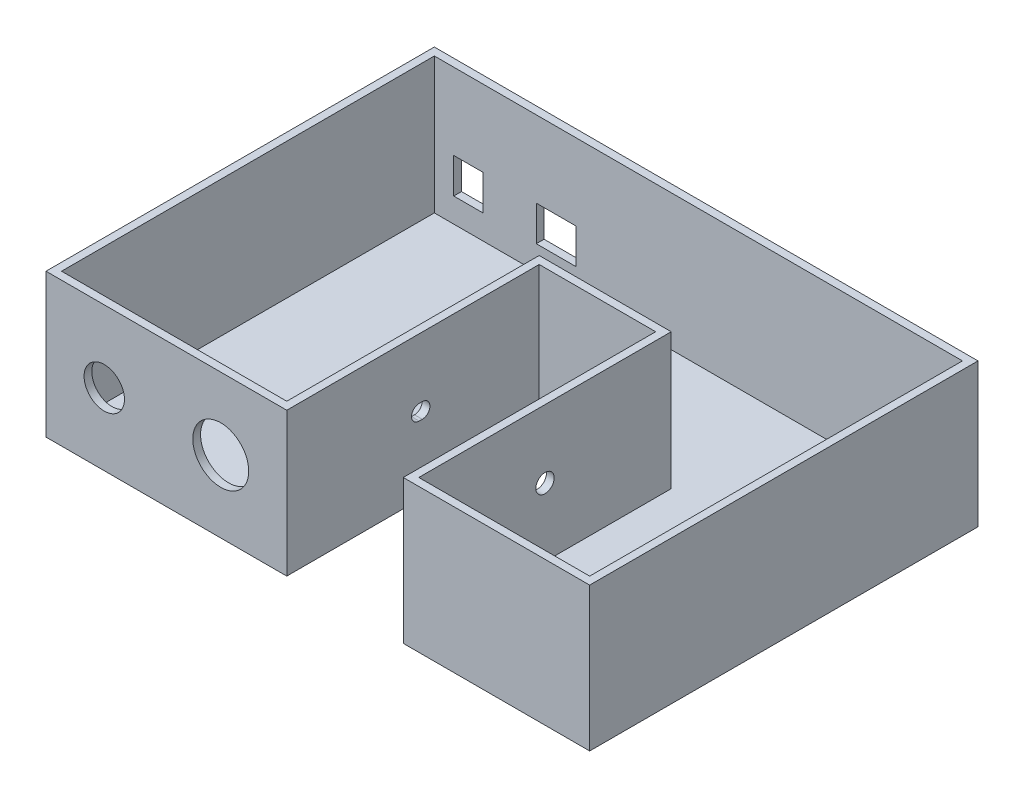
SolidWorks part; units mm, degrees
ref_plane "Front" through (0, 0, 0) normal (0, 0, 1) x (1, 0, 0)
ref_plane "Top" through (0, 0, 0) normal (0, 1, 0) x (1, 0, 0)
ref_plane "Right" through (0, 0, 0) normal (1, 0, 0) x (0, 0, -1)
sketch "Sketch1" plane through (0, 0, 0) normal (0, 1, 0) x (1, 0, 0)
  line L1 (0, 0) -> (78.74, 0)
  line L2 (0, 0) -> (0, 127)
  line L3 (0, 127) -> (78.74, 127)
  line L4 (78.74, 0) -> (78.74, 127)
  line L5 (78.74, 127) -> (116.84, 127)
  line L6 (78.74, 127) -> (78.74, 82.55)
  line L7 (78.74, 82.55) -> (116.84, 82.55)
  line L8 (116.84, 127) -> (116.84, 82.55)
  line L9 (116.84, 127) -> (177.8, 127)
  line L10 (116.84, 127) -> (116.84, 0)
  line L11 (116.84, 0) -> (177.8, 0)
  line L12 (177.8, 127) -> (177.8, 0)
  dimension "D1" = 127
  dimension "D2" = 78.74
  dimension "D3" = 38.1
  dimension "D4" = 44.45
  dimension "D5" = 127
  dimension "D6" = 60.96
extrude "Boss-Extrude1" add sketch "Sketch1" along normal blind 2.54 contours L1 L4 L3 L2 | L8 L5 L4 L7 | L12 L9 L8 L10 L11
sketch "Sketch2" plane through (0, 2.54, 0) normal (0, 1, 0) x (1, 0, 0)
  line L0 (119.38, 2.54) -> (175.26, 2.54)
  line L1 (0, 0) -> (78.74, 0) construction
  line L2 (2.54, 124.46) -> (175.26, 124.46)
  line L3 (2.54, 124.46) -> (2.54, 2.54)
  line L4 (2.54, 2.54) -> (76.2, 2.54)
  line L5 (76.2, 85.09) -> (76.2, 2.54)
  line L6 (116.84, 0) -> (177.8, 0) construction
  line L7 (175.26, 124.46) -> (175.26, 2.54)
  line L8 (78.74, 0) -> (78.74, 82.55) construction
  line L9 (119.38, 85.09) -> (119.38, 2.54)
  line L10 (0, 0) -> (0, 127) construction
  line L11 (0, 127) -> (177.8, 127) construction
  line L12 (177.8, 127) -> (177.8, 0) construction
  line L13 (116.84, 82.55) -> (116.84, 0) construction
  line L14 (0, 127) -> (0, 0)
  line L15 (0, 0) -> (78.74, 0)
  line L16 (78.74, 0) -> (78.74, 82.55)
  line L17 (78.74, 82.55) -> (116.84, 82.55)
  line L19 (76.2, 85.09) -> (119.38, 85.09)
  line L20 (78.74, 82.55) -> (116.84, 82.55) construction
  line L21 (116.84, 82.55) -> (116.84, 0)
  line L22 (116.84, 0) -> (177.8, 0)
  line L23 (177.8, 0) -> (177.8, 127)
  line L24 (177.8, 127) -> (0, 127)
  point P18 (116.84, 41.275)
  dimension "D1" = 2.54
  dimension "D2" = 2.54
  dimension "D3" = 2.54
  dimension "D4" = 2.54
  dimension "D5" = 2.54
  dimension "D6" = 2.54
  dimension "D7" = 2.54
  dimension "D8" = 2.54
extrude "Boss-Extrude2" add sketch "Sketch2" along normal blind 44.45
sketch "Sketch3" plane through (0, 0, -127) normal (0, 0, -1) x (-1, 0, 0)
  line L0 (0, 46.99) -> (0, 0) construction
  line L1 (-8.89, 21.99) -> (-18.39, 21.99)
  line L2 (-8.89, 21.99) -> (-8.89, 10.49)
  line L3 (-8.89, 10.49) -> (-18.39, 10.49)
  line L4 (-18.39, 21.99) -> (-18.39, 10.49)
  line L6 (0, 0) -> (-177.8, 0) construction
  line L10 (-35.89, 10.49) -> (-48.89, 10.49)
  line L11 (-35.89, 10.49) -> (-35.89, 21.99)
  line L12 (-35.89, 21.99) -> (-48.89, 21.99)
  line L13 (-48.89, 10.49) -> (-48.89, 21.99)
  dimension "D1" = 8.89
  dimension "D2" = 10.49
  dimension "D3" = 9.5
  dimension "D4" = 11.5
  dimension "D5" = 17.5
  dimension "D6" = 10.49
  dimension "D7" = 13
  dimension "D8" = 11.5
extrude "Cut-Extrude1" cut sketch "Sketch3" against normal up to next
sketch "Sketch5" plane through (76.2, 0, 0) normal (-1, 0, 0) x (0, 0, 1)
  line L0 (-44.315, 24.765) -> (-43.315, 24.765) construction
  line L1 (-2.54, 46.99) -> (-85.09, 46.99) construction
  line L2 (-85.09, 46.99) -> (-85.09, 2.54) construction
  line L3 (-44.315, 27.265) -> (-43.315, 27.265)
  line L4 (-44.315, 22.265) -> (-43.315, 22.265)
  arc A1 (-44.315, 27.265) -> (-44.315, 22.265) centre (-44.315, 24.765) ccw
  arc A2 (-43.315, 22.265) -> (-43.315, 27.265) centre (-43.315, 24.765) ccw
  point P1 (-43.815, 46.99)
  point P2 (-43.815, 24.765)
  point P10 (-85.09, 24.765)
  point P15 (-46.815, 24.765)
  point P16 (-40.815, 24.765)
  point P17 (-43.815, 27.265)
  point P18 (-43.815, 22.265)
  dimension "D2" = 6
  dimension "D3" = 5
extrude "Cut-Extrude2" cut sketch "Sketch5" against normal up to next
sketch "Sketch6" plane through (119.38, 0, 0) normal (1, 0, 0) x (0, 0, -1)
  line L0 (85.09, 46.99) -> (2.54, 46.99) construction
  line L1 (85.09, 46.99) -> (85.09, 2.54) construction
  circle A0 centre (43.815, 24.765) radius 3
  point P5 (43.815, 46.99)
  point P8 (85.09, 24.765)
  dimension "D1" = 6
extrude "Cut-Extrude3" cut sketch "Sketch6" against normal up to next
sketch "Sketch8" plane through (0, 2.54, 0) normal (0, 1, 0) x (1, 0, 0)
  line L0 (175.26, 124.46) -> (2.54, 124.46) construction
  line L1 (2.54, 124.46) -> (2.54, 2.54) construction
  line L2 (175.26, 124.46) -> (2.54, 124.46) construction
  circle A0 centre (5.84, 104.26) radius 1.6
  circle A1 centre (10.54, 52.36) radius 1.6
  circle A2 centre (38.44, 52.36) radius 1.6
  circle A3 centre (53.64, 103.16) radius 1.6
  dimension "D1" = 3.2
  dimension "D4" = 3.2
  dimension "D7" = 3.2
  dimension "D10" = 3.2
  dimension "D2" = 20.2
  dimension "D3" = 3.3
  dimension "D5" = 51.9
  dimension "D6" = 8
  dimension "D8" = 27.9
  dimension "D9" = 51.9
  dimension "D11" = 47.8
  dimension "D12" = 21.3
sketch "Sketch27" plane through (0, 0, 0) normal (-1, 0, 0) x (0, 0, 1)
  line L0 (-127, 46.99) -> (-127, 0) construction
  circle A0 centre (-101.6, 23.495) radius 3.81
  circle A1 centre (-88.9, 23.495) radius 3.81
  point P7 (-127, 23.495)
  dimension "D1" = 7.62
  dimension "D2" = 7.62
  dimension "D3" = 12.7
  dimension "D4" = 25.4
sketch "Sketch28" plane through (177.8, 0, 0) normal (1, 0, 0) x (0, 0, -1)
  line L0 (19.05, 23.495) -> (31.75, 23.495) construction
  line L1 (19.05, 27.305) -> (31.75, 27.305)
  line L2 (19.05, 19.685) -> (31.75, 19.685)
  line L3 (0, 46.99) -> (0, 0) construction
  arc A0 (19.05, 27.305) -> (19.05, 19.685) centre (19.05, 23.495) ccw
  arc A1 (31.75, 19.685) -> (31.75, 27.305) centre (31.75, 23.495) ccw
  point P2 (25.4, 23.495)
  point P9 (0, 23.495)
  dimension "D2" = 3.81
  dimension "D3" = 12.7
  dimension "D1" = 25.4
sketch "Sketch29" plane through (0, 0, 0) normal (0, 0, 1) x (1, 0, 0)
  line L1 (78.74, 46.99) -> (78.74, 0) construction
  line L2 (0, 46.99) -> (0, 0) construction
  circle A0 centre (57.15, 23.495) radius 9.144
  circle A1 centre (19.05, 23.495) radius 6.604
  point P11 (78.74, 23.495)
  dimension "D1" = 13.208
  dimension "D2" = 18.288
  dimension "D3" = 38.1
  dimension "D4" = 19.05
extrude "Cut-Extrude8" cut sketch "Sketch29" against normal blind 2.54
